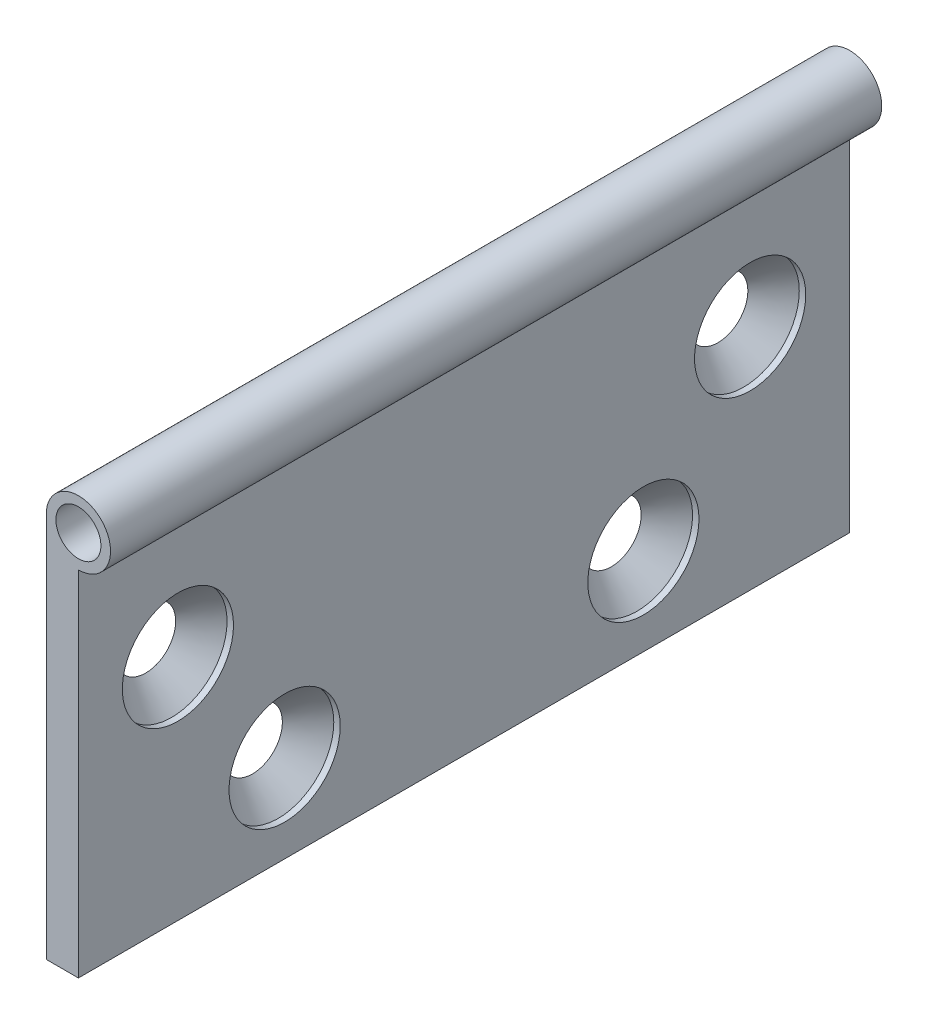
SolidWorks part; units mm, degrees
ref_plane "Front Plane" through (0, 0, 0) normal (0, 0, 1) x (1, 0, 0)
ref_plane "Top Plane" through (0, 0, 0) normal (0, 1, 0) x (1, 0, 0)
ref_plane "Right Plane" through (0, 0, 0) normal (1, 0, 0) x (0, 0, -1)
sketch "Sketch2" plane through (0, 0, 0) normal (0, 0, 1) x (1, 0, 0)
  line L0 (0, 0) -> (0, 60)
extrude "Extrude-Thin1" add sketch "Sketch2" along normal mid plane 120 thin contours L0
sketch "Sketch3" plane through (0, 0, 60) normal (0, 0, 1) x (1, 0, 0)
  circle A0 centre (5, 60) radius 5
  point P4 (5, 60)
sweep "Sweep11" add profiles "Sketch3" path edge at (5, 60, 0)
sketch "Sketch4" plane through (0, 0, 60) normal (0, 0, 1) x (1, 0, 0)
  circle A0 centre (5, 60) radius 3.5
extrude "Cut-Extrude1" cut sketch "Sketch4" against normal through all
hole_wizard "CSK for M8 Flat Head Machine Screw1" positions "Sketch5" profile "Sketch6" countersink size "M8" standard "ANSI Metric" end condition through all
sketch "Sketch5" plane through (5, 0, 0) normal (1, 0, 0) x (0, 0, -1)
  point P0 (-44.517, 35.506)
  point P2 (-27.9126, 13.6053)
sketch "Sketch6" plane through (5, 35.506, 44.517) normal (0, 1, 0) x (0, 0, -1)
  line L0 (0, 0) -> (0, 5)
  line L1 (0, 5) -> (4.5, 5)
  line L2 (4.5, 5) -> (4.5, 5.15)
  line L3 (4.5, 5.15) -> (8.65, 1)
  line L4 (8.65, 1) -> (8.65, 0)
  line L6 (8.65, 0) -> (0, 0)
  line L7 (-4.5, 5.15) -> (-8.65, 1) construction
  line L11 (0, -6.35) -> (0, 107.95) construction
  dimension "Thru Hole Dia." = 9
  dimension "Thru Hole Depth" = 5
  dimension "C'Sink Dia." = 17.3
  dimension "C'Sink Angle" = 90
  dimension "Head Clearance" = 1
mirror "Mirror1" about plane through (0, 0, 0) normal (0, 0, 1) of "CSK for M8 Flat Head Machine Screw1"
sketch "layout for cuts" plane through (5, 0, 0) normal (1, 0, 0) x (0, 0, -1)
  line L0 (-36, 55) -> (-36, 65)
  line L1 (60, 55) -> (60, 65) construction
  line L2 (-60, 56) -> (60, 56)
  line L3 (-60, 56) -> (60, 56)
  line L4 (-60, 65) -> (-60, 55) construction
  line L5 (60, 55) -> (60, 65)
  line L6 (-60, 65) -> (-60, 55)
  line L7 (60, 55) -> (60, 65)
  line L8 (-60, 65) -> (-60, 55)
  line L9 (-60, 65) -> (60, 65)
  line L10 (-60, 55) -> (60, 55) construction
  line L11 (-12, 55) -> (-12, 65)
  line L12 (0, 65) -> (0, 0) construction
  line L13 (36, 55) -> (36, 65)
  line L14 (12, 55) -> (12, 65)
  dimension "D2" = 24
  dimension "D3" = 24
  dimension "D1" = 1
sketch "Sketch8" plane through (5, 0, 0) normal (1, 0, 0) x (0, 0, -1)
  line L0 (-60, 55) -> (60, 55) construction
  line L1 (-60, 55) -> (60, 55)
sketch "Sketch9" plane through (5, 0, 0) normal (1, 0, 0) x (0, 0, -1)
  line L0 (-60, 55) -> (60, 55) construction
  line L1 (-60, 55) -> (-37, 55)
  line L4 (-13, 55) -> (13, 55)
  line L5 (-37, 55) -> (-37, 65)
  line L6 (-37, 55) -> (-37, 65)
  line L7 (35, 55) -> (35, 65)
  line L8 (35, 55) -> (35, 65)
  line L9 (-13, 55) -> (-13, 65)
  line L10 (-13, 55) -> (-13, 65)
  line L11 (35, 55) -> (60, 55)
  line L12 (13, 55) -> (13, 65)
  line L13 (13, 55) -> (13, 65)
  dimension "D1" = 1
  dimension "D2" = 1
  dimension "D3" = 1
  dimension "D4" = 1
equation "\"D2@layout for cuts\"= \"D1@Extrude-Thin1\" / 5"
equation "\"D3@layout for cuts\"= \"D1@Extrude-Thin1\" / 5"
